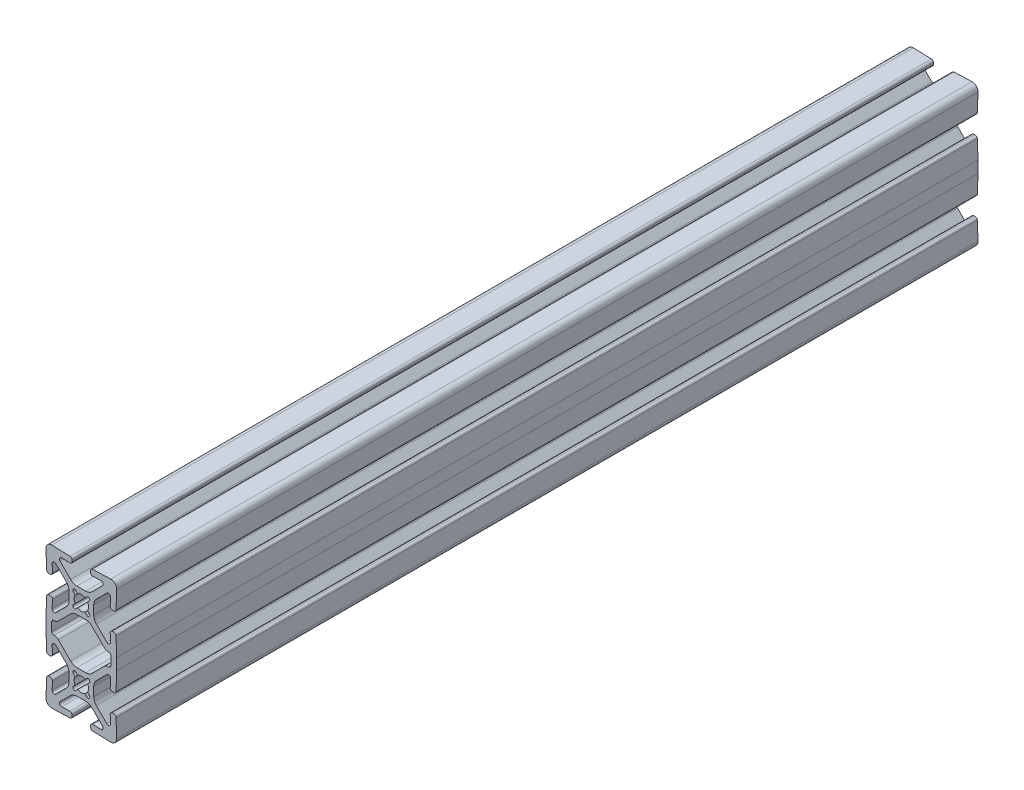
SolidWorks part; units mm, degrees
ref_plane "Front Plane" through (0, 0, 0) normal (0, 0, 1) x (1, 0, 0)
ref_plane "Top Plane" through (0, 0, 0) normal (0, 1, 0) x (1, 0, 0)
ref_plane "Right Plane" through (0, 0, 0) normal (1, 0, 0) x (0, 0, -1)
sketch "Sketch1" plane through (0, 0, 0) normal (0, 0, 1) x (1, 0, 0)
  line L0 (0, 12.5) -> (0, 25) construction
  line L1 (0, 12.5) -> (12.5, 12.5) construction
  line L2 (0, 12.5) -> (-12.5, 25) construction
  line L3 (-10.3971, 24.9988) -> (-3.9863, 24.7749)
  line L4 (-12.5, 25) -> (0, 25) construction
  line L5 (-3.2505, 23.9858) -> (-3.2689, 23.4569)
  line L6 (-4.058, 22.7211) -> (-6.948, 22.8221)
  line L10 (0, 16.88) -> (-1.5587, 16.88)
  line L11 (-3.8038, 17.8099) -> (-7.5141, 21.5202)
  line L24 (0, 12.5) -> (-12.5, 12.5) construction
  line L25 (-12.5, 12.5) -> (0, 12.5) construction
  line L26 (0, 12.5) -> (0, 0) construction
  line L27 (-12.5, 0) -> (-12.5, 25) construction
  line L28 (0, 25) -> (12.5, 25) construction
  line L29 (0, 0) -> (0, -25) construction
  line L30 (-12.5, -25) -> (12.5, -25) construction
  arc A0 (-11.9048, 24.4048) -> (-10.3971, 24.9988) centre (-10.468, 22.968) cw
  arc A4 (-3.2689, 23.4569) -> (-4.058, 22.7211) centre (-4.0314, 23.4836) cw
  arc A5 (-3.9863, 24.7749) -> (-3.2505, 23.9858) centre (-4.0129, 24.0125) cw
  arc A6 (-1.5587, 16.88) -> (-3.8038, 17.8099) centre (-1.5587, 20.055) cw
  circle A16 centre (0, 12.5) radius 2.55
  arc A18 (-7.5141, 21.5202) -> (-6.948, 22.8221) centre (-6.9746, 22.0596) cw
  circle A19 centre (-2.3794, 14.8794) radius 0.635 construction
  point P15 (0, 0)
  point P35 (-3.2956, 22.6945)
  point P38 (-3.2238, 24.7483)
  point P42 (-2.8739, 16.88)
  point P80 (-12.5, 12.5)
  point P85 (0, 0)
  point P88 (0, 0)
  dimension "D11" = 2.032
  dimension "D15" = 3.175
  dimension "Center Hole Diameter" = 5.1
  dimension "D6" = 1.27
  dimension "D1" = 45
  dimension "D2" = 2
  dimension "Rail Width" = 25
  dimension "D10" = 2.13
  dimension "T-Slot Depth" = 8.12
  dimension "D9" = 2.055
  dimension "Rail Height" = 50
  dimension "D23" = 8.76
  dimension "D5" = 15.475
  dimension "T-Slot Width" = 6.5
  dimension "D3" = 4
sketch "Sketch2" plane through (0, 0, 0) normal (1, 0, 0) x (0, 0, -1)
  line L0 (-152.4, 0) -> (152.4, 0)
  line L1 (-152.4, -25) -> (-152.4, 25) construction
  line L2 (0, 12.5) -> (0, 25) construction
  line L3 (0, 12.5) -> (0, 25) construction
  line L4 (152.4, -25) -> (152.4, 25) construction
  point P0 (-114.9, 0)
  point P3 (0, 0)
  point P7 (114.9, 0)
  point P11 (-152.4, 0)
  dimension "D1" = 37.5
  dimension "Representative Length" = 304.8
sketch "Sketch3" plane through (0, 0, 0) normal (0, 0, 1) x (1, 0, 0)
  line L1 (0, 12.5) -> (-12.5, 25) construction
  line L2 (0, 12.5) -> (-12.5, 25) construction
  line L3 (-4.38, 12.5) -> (-2.55, 12.5) construction
  line L4 (-4.38, 10.9413) -> (-4.38, 14.0587)
  line L5 (-10.3971, 24.9988) -> (-3.9863, 24.7749) construction
  line L6 (-3.2505, 23.9858) -> (-3.2689, 23.4569) construction
  line L7 (-4.058, 22.7211) -> (-6.948, 22.8221) construction
  line L12 (-5.3099, 16.3038) -> (-9.0202, 20.0141)
  line L13 (-10.2211, 16.558) -> (-10.3221, 19.448)
  line L14 (-11.4858, 15.7505) -> (-10.9569, 15.7689)
  line L15 (-12.4988, 22.8971) -> (-12.2749, 16.4863)
  line L16 (-2.8284, 14.4304) -> (-2.1953, 13.7973)
  line L17 (1.5587, 8.12) -> (-1.5587, 8.12)
  line L18 (-1.2973, 14.6953) -> (-1.9304, 15.3284)
  line L19 (-3.8038, 7.1901) -> (-8.1307, 2.8632)
  line L23 (-1.2973, 10.3047) -> (-1.9304, 9.6716)
  line L42 (-3.8038, 17.8099) -> (-7.5141, 21.5202) construction
  line L43 (0, 16.88) -> (-1.5587, 16.88) construction
  line L44 (-10.3971, 24.9988) -> (-3.9863, 24.7749)
  line L45 (-3.2505, 23.9858) -> (-3.2689, 23.4569)
  line L46 (-4.058, 22.7211) -> (-6.948, 22.8221)
  line L47 (-3.8038, 17.8099) -> (-7.5141, 21.5202)
  line L48 (1.5587, 16.88) -> (-1.5587, 16.88)
  line L59 (0, 16.88) -> (0, 15.05) construction
  line L60 (-2.8284, 10.5696) -> (-2.1953, 11.2027)
  line L61 (-12.5, 2.0675) -> (-12.2749, 8.5137)
  line L62 (-11.4858, 9.2495) -> (-10.9569, 9.2311)
  line L63 (-10.2211, 8.442) -> (-10.3221, 5.552)
  line L64 (-5.3099, 8.6962) -> (-9.0202, 4.9859)
  line L66 (10.468, 0) -> (-10.468, 0) construction
  line L67 (-10.468, 0) -> (-10.468, 1.506)
  line L68 (-9.706, 2.268) -> (-9.5675, 2.268)
  line L71 (-12.5, 0) -> (-12.5, 2.0675)
  line L72 (-12.5, 0) -> (-12.5, 25) construction
  line L76 (-12.5, 0) -> (-10.468, 0)
  line L78 (4.38, 12.5) -> (2.55, 12.5) construction
  line L79 (12.5, 0) -> (10.468, 0)
  line L80 (12.5, 0) -> (12.5, 2.0675)
  line L81 (9.706, 2.268) -> (9.5675, 2.268)
  line L82 (10.468, 0) -> (10.468, 1.506)
  line L83 (5.3099, 8.6962) -> (9.0202, 4.9859)
  line L84 (10.2211, 8.442) -> (10.3221, 5.552)
  line L85 (11.4858, 9.2495) -> (10.9569, 9.2311)
  line L86 (12.5, 2.0675) -> (12.2749, 8.5137)
  line L87 (2.8284, 10.5696) -> (2.1953, 11.2027)
  line L89 (3.8038, 17.8099) -> (7.5141, 21.5202)
  line L90 (4.058, 22.7211) -> (6.948, 22.8221)
  line L91 (3.2505, 23.9858) -> (3.2689, 23.4569)
  line L92 (10.3971, 24.9988) -> (3.9863, 24.7749)
  line L93 (1.2973, 10.3047) -> (1.9304, 9.6716)
  line L94 (3.8038, 7.1901) -> (8.1307, 2.8632)
  line L95 (1.2973, 14.6953) -> (1.9304, 15.3284)
  line L97 (2.8284, 14.4304) -> (2.1953, 13.7973)
  line L98 (12.4988, 22.8971) -> (12.2749, 16.4863)
  line L99 (11.4858, 15.7505) -> (10.9569, 15.7689)
  line L100 (10.2211, 16.558) -> (10.3221, 19.448)
  line L101 (5.3099, 16.3038) -> (9.0202, 20.0141)
  line L102 (4.38, 10.9413) -> (4.38, 14.0587)
  line L103 (0, 12.5) -> (0, 25) construction
  arc A0 (-10.3971, 24.9988) -> (-11.9048, 24.4048) centre (-10.468, 22.968) ccw construction
  arc A1 (-3.8038, 7.1901) -> (-1.5587, 8.12) centre (-1.5587, 4.945) cw
  circle A3 centre (0, 12.5) radius 2.55
  arc A5 (-10.3971, 24.9988) -> (-12.4988, 22.8971) centre (-10.468, 22.968) ccw
  arc A6 (-5.3099, 16.3038) -> (-4.38, 14.0587) centre (-7.555, 14.0587) cw
  arc A7 (-10.3221, 19.448) -> (-9.0202, 20.0141) centre (-9.5596, 19.4746) cw
  arc A8 (-10.2211, 16.558) -> (-10.9569, 15.7689) centre (-10.9836, 16.5314) cw
  arc A9 (-11.4858, 15.7505) -> (-12.2749, 16.4863) centre (-11.5125, 16.5129) cw
  circle A10 centre (-2.3794, 14.8794) radius 0.635 construction
  arc A11 (-1.9304, 15.3284) -> (-2.8284, 14.4304) centre (-2.3794, 14.8794) ccw
  arc A12 (-2.1953, 13.7973) -> (-2.1953, 11.2027) centre (0, 12.5) ccw
  arc A16 (1.2973, 10.3047) -> (-1.2973, 10.3047) centre (0, 12.5) cw
  arc A17 (-1.9304, 9.6716) -> (-2.8284, 10.5696) centre (-2.3794, 10.1206) cw
  arc A18 (-11.4858, 9.2495) -> (-12.2749, 8.5137) centre (-11.5125, 8.4871) ccw
  arc A35 (1.2973, 14.6953) -> (-1.2973, 14.6953) centre (0, 12.5) ccw
  arc A36 (-3.2505, 23.9858) -> (-3.9863, 24.7749) centre (-4.0129, 24.0125) ccw construction
  arc A37 (-4.058, 22.7211) -> (-3.2689, 23.4569) centre (-4.0314, 23.4836) ccw construction
  arc A38 (-6.948, 22.8221) -> (-7.5141, 21.5202) centre (-6.9746, 22.0596) ccw construction
  arc A39 (-3.8038, 17.8099) -> (-1.5587, 16.88) centre (-1.5587, 20.055) ccw construction
  arc A41 (-3.2505, 23.9858) -> (-3.9863, 24.7749) centre (-4.0129, 24.0125) ccw
  arc A42 (-4.058, 22.7211) -> (-3.2689, 23.4569) centre (-4.0314, 23.4836) ccw
  arc A43 (-6.948, 22.8221) -> (-7.5141, 21.5202) centre (-6.9746, 22.0596) ccw
  arc A44 (-3.8038, 17.8099) -> (-1.5587, 16.88) centre (-1.5587, 20.055) ccw
  arc A52 (-10.2211, 8.442) -> (-10.9569, 9.2311) centre (-10.9836, 8.4686) ccw
  arc A53 (-10.3221, 5.552) -> (-9.0202, 4.9859) centre (-9.5596, 5.5254) ccw
  arc A54 (-5.3099, 8.6962) -> (-4.38, 10.9413) centre (-7.555, 10.9413) ccw
  arc A55 (-10.468, 1.506) -> (-9.706, 2.268) centre (-9.706, 1.506) cw
  arc A56 (-9.5675, 2.268) -> (-8.1307, 2.8632) centre (-9.5675, 4.3) ccw
  circle A57 centre (0, 12.5) radius 2.55 construction
  arc A58 (9.5675, 2.268) -> (8.1307, 2.8632) centre (9.5675, 4.3) cw
  arc A59 (10.468, 1.506) -> (9.706, 2.268) centre (9.706, 1.506) ccw
  arc A60 (5.3099, 8.6962) -> (4.38, 10.9413) centre (7.555, 10.9413) cw
  arc A61 (10.3221, 5.552) -> (9.0202, 4.9859) centre (9.5596, 5.5254) cw
  arc A62 (10.2211, 8.442) -> (10.9569, 9.2311) centre (10.9836, 8.4686) cw
  arc A63 (3.8038, 17.8099) -> (1.5587, 16.88) centre (1.5587, 20.055) cw
  arc A64 (6.948, 22.8221) -> (7.5141, 21.5202) centre (6.9746, 22.0596) cw
  arc A65 (4.058, 22.7211) -> (3.2689, 23.4569) centre (4.0314, 23.4836) cw
  arc A66 (3.2505, 23.9858) -> (3.9863, 24.7749) centre (4.0129, 24.0125) cw
  arc A68 (11.4858, 9.2495) -> (12.2749, 8.5137) centre (11.5125, 8.4871) cw
  arc A69 (1.9304, 9.6716) -> (2.8284, 10.5696) centre (2.3794, 10.1206) ccw
  arc A71 (2.1953, 13.7973) -> (2.1953, 11.2027) centre (0, 12.5) cw
  arc A72 (1.9304, 15.3284) -> (2.8284, 14.4304) centre (2.3794, 14.8794) cw
  arc A73 (11.4858, 15.7505) -> (12.2749, 16.4863) centre (11.5125, 16.5129) ccw
  arc A74 (10.2211, 16.558) -> (10.9569, 15.7689) centre (10.9836, 16.5314) ccw
  arc A75 (10.3221, 19.448) -> (9.0202, 20.0141) centre (9.5596, 19.4746) ccw
  arc A76 (5.3099, 16.3038) -> (4.38, 14.0587) centre (7.555, 14.0587) ccw
  arc A77 (10.3971, 24.9988) -> (12.4988, 22.8971) centre (10.468, 22.968) cw
  arc A78 (3.8038, 7.1901) -> (1.5587, 8.12) centre (1.5587, 4.945) ccw
  point P40 (0, 0)
  dimension "D3" = 2.032
  dimension "D4" = 0.762
  dimension "D5" = 2.032
  dimension "D2" = 4.536
  dimension "D1" = 0
extrude "Boss-Extrude1" add sketch "Sketch3" along normal mid plane 304.8
pattern_circular "CirPattern1" count 2 over 360 about axis through (0, 0, 0) along (0, 0, 1) of "Boss-Extrude1"
ref_plane "Contact Plane 1" through (0, 25, 0) normal (0, 1, 0) x (1, 0, 0)
ref_plane "Contact Plane 2" through (12.5, 12.5, 0) normal (1, 0, 0) x (0, 0, -1)
ref_plane "Contact Plane 3" through (0, -25, 0) normal (0, -1, 0) x (-1, 0, 0)
ref_plane "Contact Plane 4" through (-12.5, 12.5, 0) normal (-1, 0, 0) x (0, 0, 1)
equation "\"D1@Sketch2\"=\"Rail Width@Sketch1\"*1.5"
equation "\"D1@Boss-Extrude1\"=\"Representative Length@Sketch2\""
